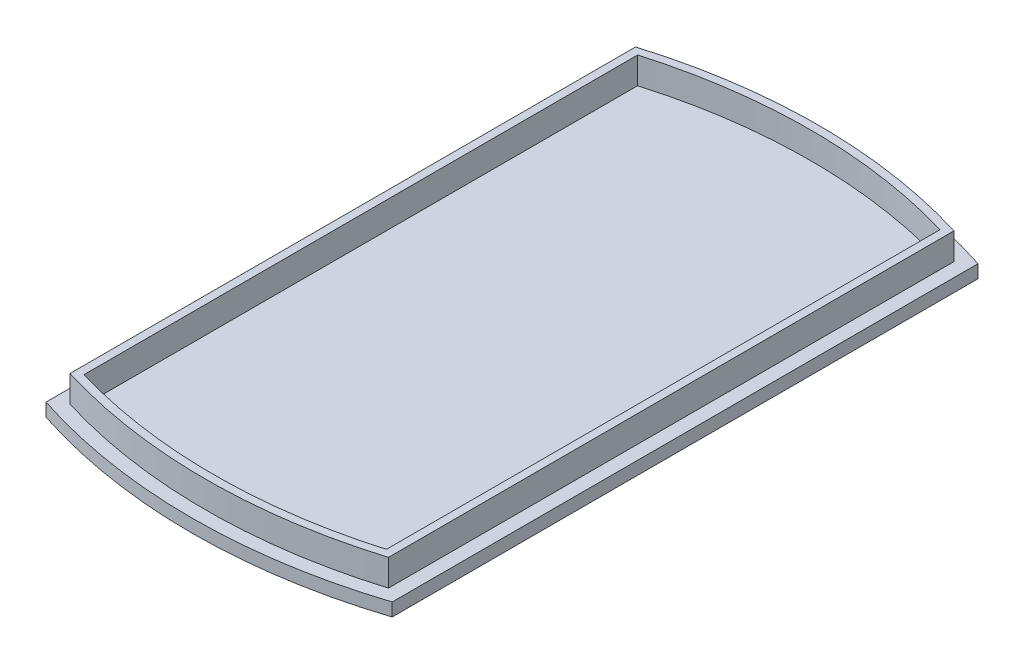
SolidWorks part; units mm, degrees
ref_plane "Front Plane" through (0, 0, 0) normal (0, 0, 1) x (1, 0, 0)
ref_plane "Top Plane" through (0, 0, 0) normal (0, 1, 0) x (1, 0, 0)
ref_plane "Right Plane" through (0, 0, 0) normal (1, 0, 0) x (0, 0, -1)
sketch "Sketch1" plane through (0, 0, 0) normal (0, 1, 0) x (1, 0, 0)
  line L0 (0, 0) -> (78.0565, 0) construction
  line L2 (-32.5, 55) -> (-32.5, -55)
  line L4 (32.5, 55) -> (32.5, -55)
  line L5 (-32.5, 55) -> (32.5, -55) construction
  line L6 (-32.5, -55) -> (32.5, 55) construction
  arc A0 (32.5, 55) -> (-32.5, 55) centre (0, -44.8436) ccw
  arc A1 (32.5, -55) -> (-32.5, -55) centre (0, 44.8436) cw
  point P0 (0, 0)
  dimension "D3" = 210
  dimension "D1" = 110
  dimension "D2" = 65
extrude "Boss-Extrude1" add sketch "Sketch1" along normal blind 7
sketch "Sketch2" plane through (0, 7, 0) normal (0, 1, 0) x (1, 0, 0)
  line L0 (28.4, -51.9771) -> (28.4, 51.9771)
  line L1 (-28.4, 51.9771) -> (-28.4, -51.9771)
  line L4 (29.9, -53.0939) -> (29.9, 53.0939)
  line L5 (-29.9, 53.0939) -> (-29.9, -53.0939)
  line L6 (29.9, -53.0939) -> (29.9, 53.0939)
  line L7 (-29.9, 53.0939) -> (-29.9, -53.0939)
  arc A0 (-28.4, -51.9771) -> (28.4, -51.9771) centre (0, 44.8436) ccw
  arc A1 (28.4, 51.9771) -> (-28.4, 51.9771) centre (0, -44.8436) ccw
  arc A4 (-29.9, -53.0939) -> (29.9, -53.0939) centre (0, 44.8436) ccw
  arc A5 (29.9, 53.0939) -> (-29.9, 53.0939) centre (0, -44.8436) ccw
  arc A6 (-29.9, -53.0939) -> (29.9, -53.0939) centre (0, 44.8436) ccw
  arc A7 (29.9, 53.0939) -> (-29.9, 53.0939) centre (0, -44.8436) ccw
  dimension "D1" = 2.6
  dimension "D2" = 1.5
extrude "Boss-Extrude2" add sketch "Sketch2" along normal blind 5
chamfer "Chamfer1" distance 12.5 angle 20 4 edges at (32.5, 0, 0) (0, 0, -60.1564) (-32.5, 0, 0) (0, 0, 60.1564)
